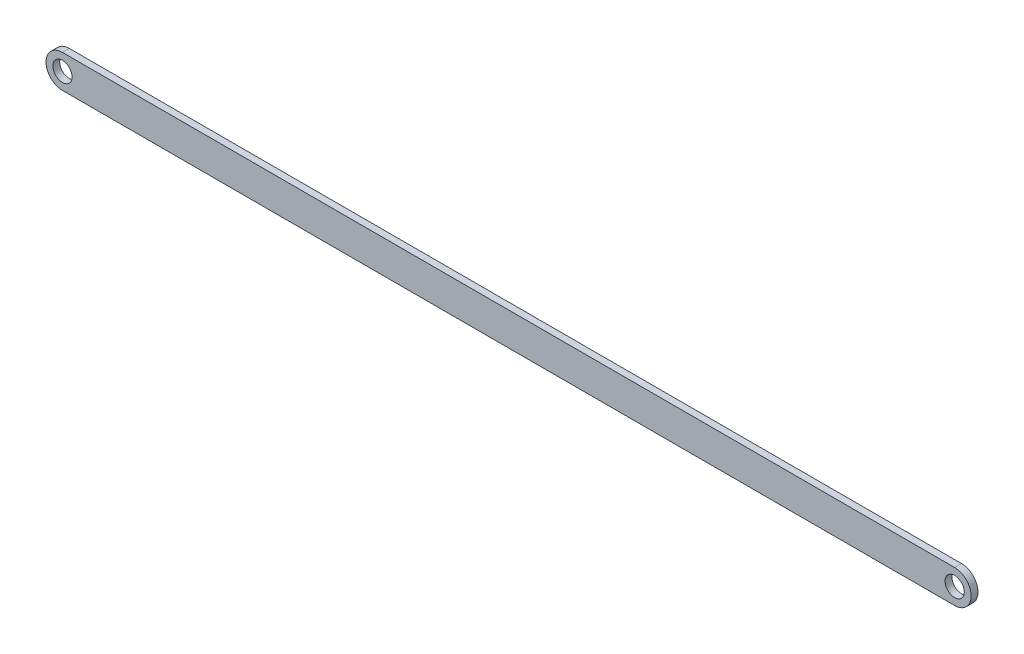
SolidWorks part; units mm, degrees
ref_plane "Płaszczyzna przednia" through (0, 0, 0) normal (0, 0, 1) x (1, 0, 0)
ref_plane "Płaszczyzna górna" through (0, 0, 0) normal (0, 1, 0) x (1, 0, 0)
ref_plane "Płaszczyzna prawa" through (0, 0, 0) normal (1, 0, 0) x (0, 0, -1)
sketch "Szkic1" plane through (0, 0, 0) normal (0, 0, 1) x (1, 0, 0)
  line L5 (0, 0) -> (650, 0)
  line L7 (0, 24) -> (650, 24)
  arc A2 (0, 24) -> (0, 0) centre (0, 12) ccw
  arc A4 (650, 0) -> (650, 24) centre (650, 12) ccw
  dimension "D1" = 650
  dimension "D2" = 24
extrude "Dodanie-wyciągnięcie1" add sketch "Szkic1" along normal blind 5
sketch "Szkic2" plane through (0, 0, 5) normal (0, 0, 1) x (1, 0, 0)
  circle A0 centre (0, 12) radius 7
  circle A1 centre (650, 12) radius 7
extrude "Wytnij-wyciągnięcie1" cut sketch "Szkic2" against normal blind 5
